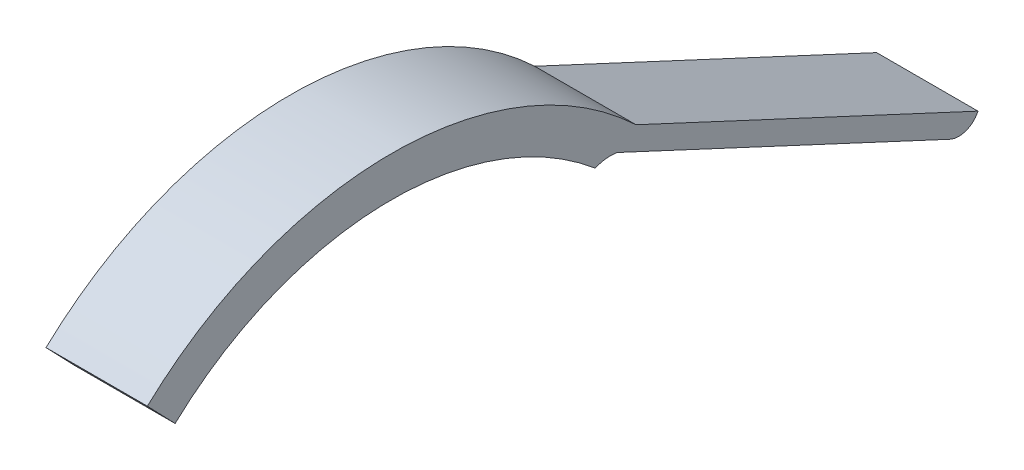
SolidWorks part; units mm, degrees
ref_plane "Front" through (0, 0, 0) normal (0, 0, 1) x (1, 0, 0)
ref_plane "Top" through (0, 0, 0) normal (0, 1, 0) x (1, 0, 0)
ref_plane "Right" through (0, 0, 0) normal (1, 0, 0) x (0, 0, -1)
sketch "Sketch1" plane through (0, 0, 0) normal (1, 0, 0) x (0, 0, -1)
  line L8 (0, 11.75) -> (0, 16.75) construction
  line L9 (9.5776, 10.3484) -> (10.3779, 10.9685)
  line L10 (-10.4937, 11.0655) -> (-8.2534, 8.7325) construction
  line L11 (10.3779, 10.9685) -> (24.8831, 4.2157)
  line L12 (23.6873, 3.7796) -> (9.5776, 10.3484)
  line L13 (-10.3497, 10.9952) -> (-9.1722, 9.7689)
  arc A1 (9.6975, 10.4413) -> (-9.801, 10.3442) centre (0, 0) ccw construction
  arc A2 (0, 15.25) -> (-10.4937, 11.0655) centre (0, 0) ccw construction
  arc A3 (8.6476, 10.2362) -> (9.5776, 10.3484) centre (9.297, 8.7635) cw
  arc A4 (24.8831, 4.2157) -> (23.6873, 3.7796) centre (24.0672, 4.5955) cw
  arc A5 (8.6476, 10.2362) -> (-9.1722, 9.7689) centre (0, 0) ccw
  arc A6 (10.3779, 10.9685) -> (-10.3497, 10.9952) centre (0, 0) ccw
  arc A7 (0, 12.4855) -> (-8.2534, 8.7325) centre (1.2066, -1.1196) ccw construction
  point P5 (0, 14.25)
  point P6 (24.3755, 3.75)
  dimension "D3" = 0.9
  dimension "D1" = 16
  dimension "D2" = 3.75
extrude "Boss-Extrude1" add sketch "Sketch1" along normal blind 4.3
